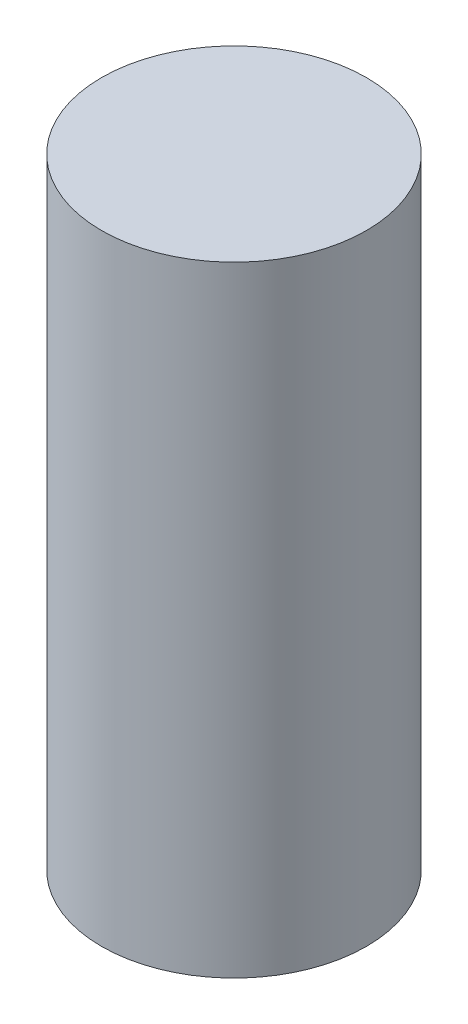
SolidWorks part; units mm, degrees
material "Custom Plastic"
ref_plane "Front Plane" through (0, 0, 0) normal (0, 0, 1) x (1, 0, 0)
ref_plane "Top Plane" through (0, 0, 0) normal (0, 1, 0) x (1, 0, 0)
ref_plane "Right Plane" through (0, 0, 0) normal (1, 0, 0) x (0, 0, -1)
sketch "Sketch1" plane through (0, 0, 0) normal (0, 1, 0) x (1, 0, 0)
  circle A0 centre (0, 0) radius 5
  dimension "D1" = 10
extrude "Boss-Extrude1" add sketch "Sketch1" along normal blind 23.4
sketch "Sketch4" plane through (0, 0, 0) normal (0, -1, 0) x (-1, 0, 0)
  circle A0 centre (0, 0) radius 2.45
  dimension "D1" = 4.9
extrude "Cut-Extrude2" cut sketch "Sketch4" against normal blind 4.69
